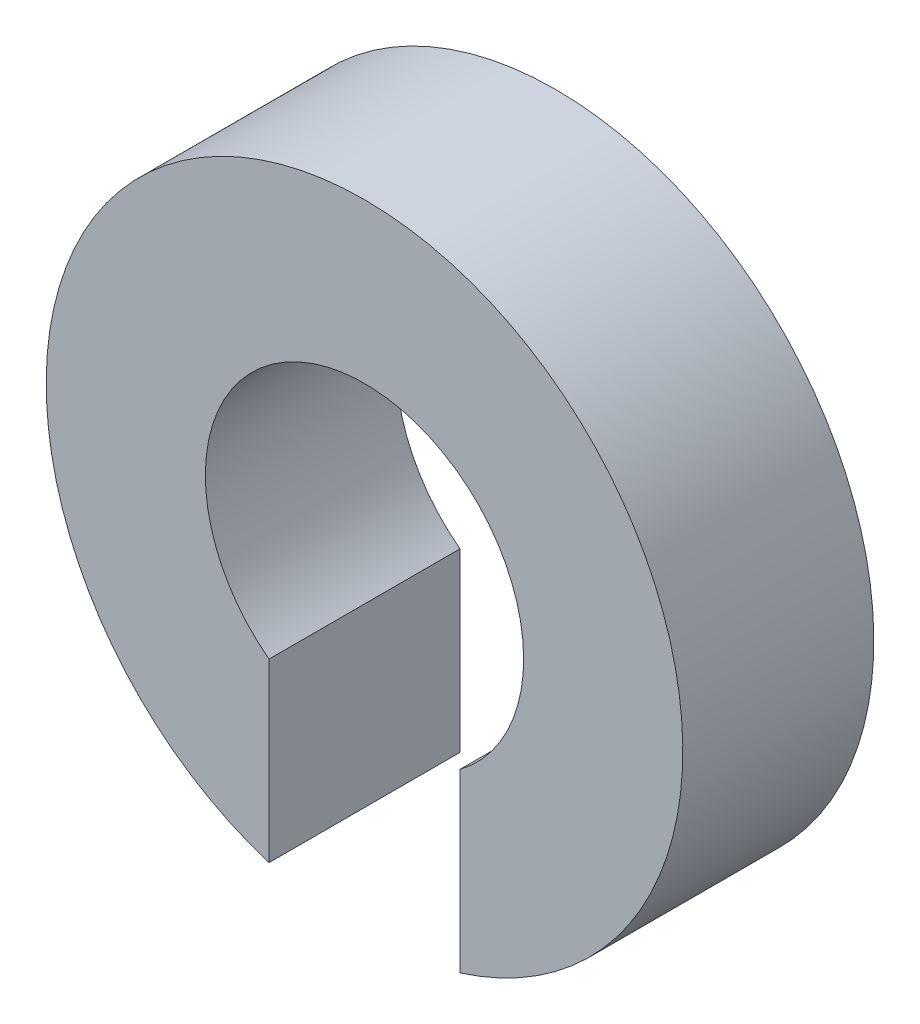
SolidWorks part; units mm, degrees
ref_plane "正面" through (0, 0, 0) normal (0, 0, 1) x (1, 0, 0)
ref_plane "平面" through (0, 0, 0) normal (0, 1, 0) x (1, 0, 0)
ref_plane "右側面" through (0, 0, 0) normal (1, 0, 0) x (0, 0, -1)
sketch "ｽｹｯﾁ1" plane through (0, 0, 0) normal (0, 0, 1) x (1, 0, 0)
  line L2 (-1.5, -4.7697) -> (-1.5, -2)
  line L4 (1.5, -4.7697) -> (1.5, -2)
  line L5 (-1.5, -8.2982) -> (1.5, -1.7018) construction
  line L6 (-1.5, -1.7018) -> (1.5, -8.2982) construction
  arc A0 (1.5, -2) -> (-1.5, -2) centre (0, 0) ccw
  arc A1 (1.5, -4.7697) -> (-1.5, -4.7697) centre (0, 0) ccw
  point P4 (0, -5)
  dimension "D1" = 5
  dimension "D2" = 10
  dimension "D3" = 3
extrude "ﾎﾞｽ - 押し出し1" add sketch "ｽｹｯﾁ1" along normal blind 3
